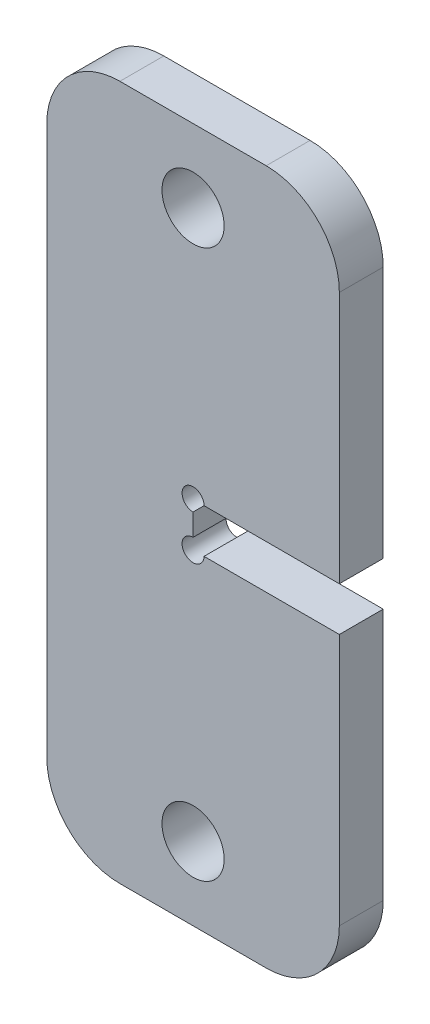
SolidWorks part; units mm, degrees
material "Plain Carbon Steel"
ref_plane "Front Plane" through (0, 0, 0) normal (0, 0, 1) x (1, 0, 0)
ref_plane "Top Plane" through (0, 0, 0) normal (0, 1, 0) x (1, 0, 0)
ref_plane "Right Plane" through (0, 0, 0) normal (1, 0, 0) x (0, 0, -1)
sketch "Sketch1" plane through (0, 0, 0) normal (0, 0, 1) x (1, 0, 0)
  line L0 (691, 395) -> (691, 300) construction
  line L1 (691, 347.5) -> (711, 347.5) construction
  line L2 (711, 350.5) -> (711, 385)
  line L3 (691, 350.5) -> (711, 350.5)
  line L4 (671, 385) -> (671, 310)
  line L5 (701, 395) -> (681, 395)
  line L6 (711, 310) -> (711, 385)
  line L7 (681, 300) -> (701, 300)
  line L8 (671, 385) -> (671, 310)
  line L9 (701, 395) -> (681, 395)
  line L10 (711, 310) -> (711, 344.5)
  line L11 (681, 300) -> (701, 300)
  line L12 (691, 350.5) -> (691, 344.5)
  line L13 (691, 344.5) -> (711, 344.5)
  line L15 (691, 350.5) -> (711, 344.5) construction
  line L16 (691, 344.5) -> (711, 350.5) construction
  circle A6 centre (691, 310) radius 4.25 construction
  circle A7 centre (691, 385) radius 4.25 construction
  arc A8 (681, 395) -> (671, 385) centre (681, 385) ccw
  arc A9 (711, 385) -> (701, 395) centre (701, 385) ccw
  arc A10 (701, 300) -> (711, 310) centre (701, 310) ccw
  arc A11 (671, 310) -> (681, 300) centre (681, 310) ccw
  arc A12 (681, 395) -> (671, 385) centre (681, 385) ccw
  arc A13 (711, 385) -> (701, 395) centre (701, 385) ccw
  arc A14 (701, 300) -> (711, 310) centre (701, 310) ccw
  arc A15 (671, 310) -> (681, 300) centre (681, 310) ccw
  circle A16 centre (691, 310) radius 4.25
  circle A17 centre (691, 385) radius 4.25
  point P10 (701, 347.5)
  dimension "D1" = 0
  dimension "D2" = 6
extrude "Boss-Extrude1" add sketch "Sketch1" along normal blind 6
sketch "Sketch3" plane through (0, 0, 6) normal (0, 0, 1) x (1, 0, 0)
  line L0 (691, 344.5) -> (691, 350.5) construction
  line L1 (691, 350.5) -> (711, 350.5) construction
  circle A0 centre (691, 350.5) radius 1.5
  circle A1 centre (691, 344.5) radius 1.5
  dimension "D1" = 3
  dimension "D2" = 3
extrude "Cut-Extrude1" cut sketch "Sketch3" against normal through all
